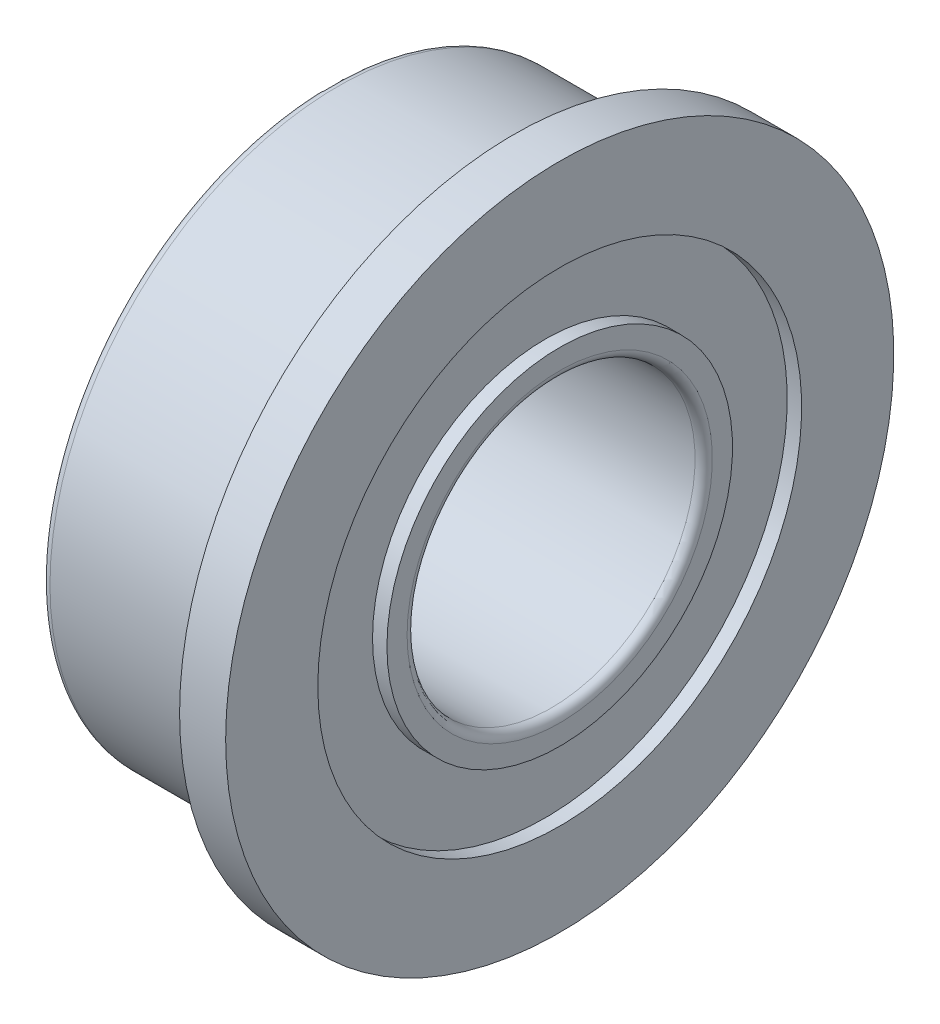
SolidWorks part; units mm, degrees
ref_plane "Front Plane" through (0, 0, 0) normal (0, 0, 1) x (1, 0, 0)
ref_plane "Top Plane" through (0, 0, 0) normal (0, 1, 0) x (1, 0, 0)
ref_plane "Right Plane" through (0, 0, 0) normal (1, 0, 0) x (0, 0, -1)
sketch "Sketch1" plane through (0, 0, 0) normal (0, 0, 1) x (1, 0, 0)
  line L0 (-3.2, 0) -> (0.8, 0) construction
  line L1 (0, 5.2) -> (0, 5.8)
  line L2 (0, 5.8) -> (0.8, 5.8)
  line L3 (0.8, 5.8) -> (0.8, 4.2)
  line L4 (0.8, 2.5) -> (-3.2, 2.5)
  line L5 (-3.2, 2.5) -> (-3.2, 3)
  line L6 (-3.2, 5) -> (-0.2, 5)
  line L7 (-3.2, 4.2) -> (-2.95, 4.2)
  line L8 (-2.95, 4.2) -> (-2.95, 3)
  line L9 (-2.95, 3) -> (-3.2, 3)
  line L10 (0.8, 4.2) -> (0.55, 4.2)
  line L11 (0.55, 4.2) -> (0.55, 3)
  line L12 (0.55, 3) -> (0.8, 3)
  line L13 (-3.2, 4.2) -> (-3.2, 5)
  line L14 (0.8, 3) -> (0.8, 2.5)
  arc A0 (-0.2, 5) -> (0, 5.2) centre (0, 5) ccw
  dimension "FIX_1" = 0.2
  dimension "D_s" = 5
  dimension "C" = 0.8
  dimension "MSM_2" = 6
  dimension "MSM_1" = 8.4
  dimension "D" = 10
  dimension "D1." = 11.6
  dimension "B" = 4
  dimension "MSM_3" = 0.25
revolve "Revolve1" add sketch "Sketch1" angle 360 about L0
fillet "Fillet1" radius 0.15 3 edges at (0.8, 0, 2.5) (-3.2, 0, 2.5) (-3.2, 0, 5)
